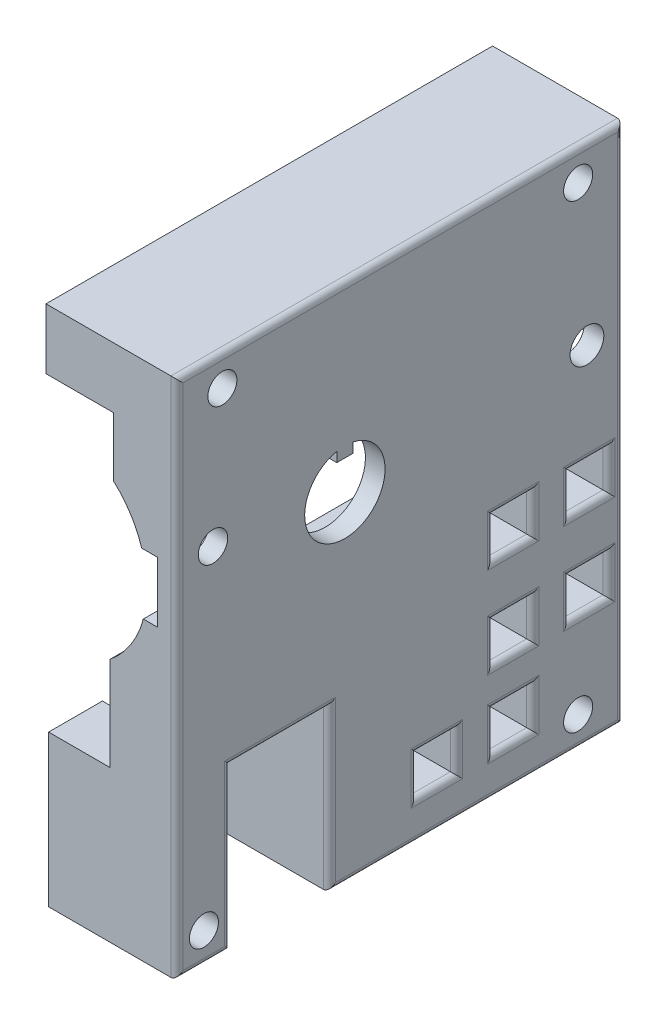
SolidWorks part; units mm, degrees
ref_plane "Front" through (0, 0, 0) normal (0, 0, 1) x (1, 0, 0)
ref_plane "Top" through (0, 0, 0) normal (0, 1, 0) x (1, 0, 0)
ref_plane "Right" through (0, 0, 0) normal (1, 0, 0) x (0, 0, -1)
sketch "Profile" plane through (0, 0, 0) normal (0, 0, 1) x (1, 0, 0)
  line L0 (-6.0107, -58.6279) -> (-6.0107, -33.6279)
  line L1 (-6.0107, -58.6279) -> (15.1893, -58.6279)
  line L2 (-6.4407, 17.4121) -> (-6.4407, 27.4121)
  line L3 (-6.4407, 27.4121) -> (15.1893, 27.4121)
  line L4 (15.1893, -58.6279) -> (15.1893, 27.4121)
  line L5 (-6.0107, -33.6279) -> (4.1393, -33.6279)
  line L6 (4.1393, -33.6279) -> (4.1393, -18.1379)
  line L7 (9.6313, -9.6379) -> (11.9493, -9.6379)
  line L8 (11.9493, -9.6379) -> (11.9493, 0.3621)
  line L9 (9.3593, 0.3621) -> (11.9493, 0.3621)
  line L10 (4.7093, 17.4121) -> (4.7093, 7.6371)
  line L11 (4.7093, 17.4121) -> (-6.4407, 17.4121)
  arc A0 (9.3593, 0.3621) -> (4.7093, 7.6371) centre (-6.1754, -4.4437) ccw
  arc A1 (4.1393, -18.1379) -> (9.6313, -9.6379) centre (-6.0948, -5.5013) ccw
  dimension "D14" = 16.261
  dimension "D17" = 16.261
  dimension "D2" = 10
  dimension "D3" = 2.59
  dimension "D4" = 2.318
  dimension "D5" = 9.775
  dimension "D6" = 11.15
  dimension "D7" = 15.49
  dimension "D8" = 10.15
  dimension "D9" = 25
  dimension "D10" = 21.2
  dimension "D11" = 86.04
  dimension "D12" = 21.63
  dimension "D13" = 10
  dimension "D15" = 23.99
  dimension "D16" = 5.492
extrude "ProfileExtrude" add sketch "Profile" along normal blind 73.76
sketch "HoseWindow" plane through (15.1893, 0, 0) normal (1, 0, 0) x (0, 0, -1)
  line L0 (-73.76, -58.6279) -> (0, -58.6279) construction
  line L1 (-64.87, -58.6279) -> (-48.58, -58.6279)
  line L2 (-64.87, -58.6279) -> (-64.87, -32.1279)
  line L3 (-64.87, -32.1279) -> (-48.58, -32.1279)
  line L4 (-48.58, -58.6279) -> (-48.58, -32.1279)
  line L5 (-73.76, -58.6279) -> (-73.76, 27.4121) construction
  dimension "D1" = 16.29
  dimension "D2" = 26.5
  dimension "D3" = 8.89
extrude "HoseWindowCut" cut sketch "HoseWindow" against normal through all
sketch "CageScrews" plane through (15.1893, 0, 0) normal (1, 0, 0) x (0, 0, -1)
  line L0 (-73.76, 27.4121) -> (0, 27.4121) construction
  line L1 (-73.76, -58.6279) -> (-73.76, 27.4121) construction
  line L2 (0, -58.6279) -> (0, 27.4121) construction
  line L3 (-48.58, -58.6279) -> (0, -58.6279) construction
  line L4 (-73.76, -58.6279) -> (-64.87, -58.6279) construction
  circle A0 centre (-66.26, 22.4121) radius 2.4
  circle A1 centre (-7.5, 22.4121) radius 2.4
  circle A2 centre (-7.5, -53.6279) radius 2.4
  circle A3 centre (-69.31, -53.6279) radius 2.4
  dimension "D1" = 4.8
  dimension "D2" = 4.8
  dimension "D3" = 4.8
  dimension "D4" = 4.8
  dimension "D5" = 5
  dimension "D6" = 7.5
  dimension "D7" = 7.5
  dimension "D8" = 5
  dimension "D9" = 5
  dimension "D10" = 7.5
  dimension "D11" = 5
  dimension "D12" = 4.45
extrude "CageScrewsCut" cut sketch "CageScrews" against normal through all
sketch "AxleHole" plane through (15.1893, 0, 0) normal (1, 0, 0) x (0, 0, -1)
  line L0 (-46.03, 2.3073) -> (-46.03, -9.2169) construction
  line L1 (-44.699, 2.3073) -> (-47.361, 2.3073)
  line L2 (-47.361, 2.3073) -> (-47.361, 3.9263)
  line L3 (-44.699, 2.3073) -> (-44.699, 3.9263)
  line L4 (-48.58, -58.6279) -> (0, -58.6279) construction
  line L5 (0, -58.6279) -> (0, 27.4121) construction
  arc A0 (-47.361, 3.9263) -> (-44.699, 3.9263) centre (-46.03, -2.5779) ccw
  dimension "D1" = 13.278
  dimension "D2" = 1.619
  dimension "D3" = 1.619
  dimension "D4" = 1.331
  dimension "D5" = 56.05
  dimension "D6" = 46.03
extrude "AxleHoleCut" cut sketch "AxleHole" against normal through all
sketch "SetScrews" plane through (15.1893, 0, 0) normal (1, 0, 0) x (0, 0, -1)
  line L0 (-46.03, -9.2169) -> (-46.03, -2.5779) construction
  circle A0 centre (-67.8072, 0.5449) radius 2.4263
  circle A1 centre (-6.043, -1.5582) radius 2.7888
  arc A3 (-47.361, 3.9263) -> (-44.699, 3.9263) centre (-46.03, -2.5779) ccw construction
  dimension "D1" = 22
  dimension "D2" = 40
extrude "SetScrewsCut" cut sketch "SetScrews" against normal through all
sketch "Sketch1" plane through (15.1893, 0, 0) normal (1, 0, 0) x (0, 0, -1)
  line L0 (-21.5, -45.7779) -> (-21.5, -52.2779)
  line L1 (-21.5, -45.7779) -> (-15, -45.7779)
  line L2 (-21.5, -52.2779) -> (-15, -52.2779)
  line L3 (-15, -45.7779) -> (-15, -52.2779)
  line L4 (0, -58.6279) -> (0, 27.4121) construction
  line L5 (-48.58, -58.6279) -> (0, -58.6279) construction
  line L6 (-34.1, -45.7779) -> (-27.6, -45.7779)
  line L7 (-34.1, -52.2779) -> (-27.6, -52.2779)
  line L8 (-34.1, -45.7779) -> (-34.1, -52.2779)
  line L9 (-27.6, -45.7779) -> (-27.6, -52.2779)
  line L10 (-8.9, -33.0779) -> (-2.4, -33.0779)
  line L11 (-8.9, -39.5779) -> (-2.4, -39.5779)
  line L12 (-8.9, -33.0779) -> (-8.9, -39.5779)
  line L13 (-2.4, -33.0779) -> (-2.4, -39.5779)
  line L14 (-21.5, -33.0779) -> (-15, -33.0779)
  line L15 (-21.5, -39.5779) -> (-15, -39.5779)
  line L16 (-21.5, -33.0779) -> (-21.5, -39.5779)
  line L17 (-15, -33.0779) -> (-15, -39.5779)
  line L18 (-21.5, -45.7779) -> (-34.1, -45.7779) construction
  line L19 (-8.9, -18.0779) -> (-2.4, -18.0779)
  line L20 (-8.9, -24.5779) -> (-2.4, -24.5779)
  line L21 (-8.9, -18.0779) -> (-8.9, -24.5779)
  line L22 (-2.4, -18.0779) -> (-2.4, -24.5779)
  line L23 (-21.5, -18.0779) -> (-15, -18.0779)
  line L24 (-21.5, -24.5779) -> (-15, -24.5779)
  line L25 (-21.5, -18.0779) -> (-21.5, -24.5779)
  line L26 (-15, -18.0779) -> (-15, -24.5779)
  line L27 (-21.5, -33.0779) -> (-8.9, -33.0779) construction
  line L42 (-34.1, -33.0779) -> (-27.6, -33.0779) [skipped]
  line L43 (-34.1, -39.5779) -> (-27.6, -39.5779) [skipped]
  line L44 (-34.1, -33.0779) -> (-34.1, -39.5779) [skipped]
  line L45 (-27.6, -33.0779) -> (-27.6, -39.5779) [skipped]
  dimension "D1" = 15
  dimension "D2" = 6.5
  dimension "D3" = 6.5
  dimension "D4" = 6.35
  dimension "D5" = 12.6
  dimension "D6" = 12.6
extrude "Cut-Extrude1" cut sketch "Sketch1" against normal through all
fillet "Fillet1" radius 1 32 edges at (15.1893, -49.0279, 21.5) (15.1893, -52.2779, 18.25) (15.1893, -49.0279, 15) (15.1893, -45.7779, 18.25) (15.1893, -58.6279, 69.315) (15.1893, -45.3779, 64.87) (15.1893, -32.1279, 56.725) (15.1893, -45.3779, 48.58) (15.1893, -58.6279, 24.29) (15.1893, -15.6079, 0) (15.1893, 27.4121, 36.88) (15.1893, -15.6079, 73.76) (15.1893, -24.5779, 5.65) (15.1893, -21.3279, 2.4) (15.1893, -18.0779, 5.65) (15.1893, -21.3279, 8.9) (15.1893, -21.3279, 15) (15.1893, -18.0779, 18.25) (15.1893, -21.3279, 21.5) (15.1893, -24.5779, 18.25) (15.1893, -39.5779, 5.65) (15.1893, -36.3279, 2.4) (15.1893, -33.0779, 5.65) (15.1893, -36.3279, 8.9) (15.1893, -36.3279, 15) (15.1893, -33.0779, 18.25) (15.1893, -36.3279, 21.5) (15.1893, -39.5779, 18.25) (15.1893, -52.2779, 30.85) (15.1893, -49.0279, 27.6) (15.1893, -45.7779, 30.85) (15.1893, -49.0279, 34.1)
equation "\"BottomEdge\"=21.20mm"
equation "\"TopEdge\"=21.63mm"
equation "\"TotalHeight\"=86.04mm"
equation "\"TotalLength\"=73.76mm"
equation "\"Screw Clearance\" = 10mm"
equation "\"TopDepth\"= 11.15mm"
equation "\"BottomDepth\"=10.15mm"
equation "\"TopHeight\"=9.775mm"
equation "\"BottomHeight\"=15.49mm"
equation "\"TopChannelDepth\"=2.59mm"
equation "\"BottomChannelDepth\"=2.318mm"
equation "\"ChannelHeight\"=10mm"
equation "\"ChamberRadius\"=16.261mm"
equation "\"ChanRelHeight\"=23.99mm"
equation "\"ChanRelDepth\"=5.492mm"
equation "\"D2@Profile\"= \"ChannelHeight\""
equation "\"D4@Profile\"= \"BottomChannelDepth\""
equation "\"D3@Profile\"= \"TopChannelDepth\""
equation "\"D5@Profile\"= \"TopHeight\""
equation "\"D7@Profile\"= \"BottomHeight\""
equation "\"ScrewClearanceBottom\" = 25mm"
equation "\"D9@Profile\"=\"ScrewClearanceBottom\""
equation "\"D13@Profile\"= \"Screw Clearance\""
equation "\"D8@Profile\"= \"BottomDepth\""
equation "\"D6@Profile\"= \"TopDepth\""
equation "\"D10@Profile\"=\"BottomEdge\""
equation "\"D12@Profile\"= \"TopEdge\""
equation "\"D11@Profile\"= \"TotalHeight\""
equation "\"D15@Profile\"= \"ChanRelHeight\""
equation "\"D16@Profile\"= \"ChanRelDepth\""
equation "\"D17@Profile\"= \"ChamberRadius\""
equation "\"D14@Profile\"= \"ChamberRadius\""
equation "\"D1@ProfileExtrude\"= \"TotalLength\""
equation "\"CageScrewDiameter\"=4.8mm"
equation "\"SetScrewDiameter\"=3.5mm"
equation "\"AxleRadius\"=6.639mm"
equation "\"KeyHeight\"=1.619mm"
equation "\"KeyWidth\"=2.662mm"
equation "\"HoseWindowWidth\"=16.29mm"
equation "\"HoseWindowHeight\"=26.5mm"
equation "\"HoseWindow-Edge\"=8.89mm"
equation "\"CageScrew-VerticalEdge\"=5.0mm"
equation "\"CageScrew-HorizontalEdge\"=7.5mm"
equation "\"CageScrew-HoseCornerScrewEdge\"=4.45mm"
equation "\"Axle-BottomEdge\"=56.05mm"
equation "\"Axle-FrontEdge\"=46.03mm"
equation "\"FrontSetScrew-Axel\"=40mm"
equation "\"D1@HoseWindow\"= \"HoseWindowWidth\""
equation "\"D2@HoseWindow\"= \"HoseWindowHeight\""
equation "\"D3@HoseWindow\"= \"HoseWindow-Edge\""
equation "\"D6@CageScrews\"= \"CageScrew-HorizontalEdge\""
equation "\"D7@CageScrews\"= \"CageScrew-HorizontalEdge\""
equation "\"D10@CageScrews\"= \"CageScrew-HorizontalEdge\""
equation "\"D12@CageScrews\"= \"CageScrew-HoseCornerScrewEdge\""
equation "\"D5@CageScrews\"= \"CageScrew-VerticalEdge\""
equation "\"D8@CageScrews\"= \"CageScrew-VerticalEdge\""
equation "\"D11@CageScrews\"= \"CageScrew-VerticalEdge\""
equation "\"D9@CageScrews\"= \"CageScrew-VerticalEdge\""
equation "\"D1@CageScrews\"= \"CageScrewDiameter\""
equation "\"D2@CageScrews\"= \"CageScrewDiameter\""
equation "\"D4@CageScrews\"= \"CageScrewDiameter\""
equation "\"D3@CageScrews\"= \"CageScrewDiameter\""
equation "\"D1@AxleHole\"= \"AxleRadius\" * 2"
equation "\"D3@AxleHole\"= \"KeyHeight\""
equation "\"D2@AxleHole\"= \"KeyHeight\""
equation "\"D4@AxleHole\"= \"KeyWidth\" / 2"
equation "\"D6@AxleHole\"= \"Axle-FrontEdge\""
equation "\"D5@AxleHole\"= \"Axle-BottomEdge\""
equation "\"D2@SetScrews\"= \"FrontSetScrew-Axel\""
equation "\"BackSetScrew-Axel\"=22mm"
equation "\"D1@SetScrews\"= \"BackSetScrew-Axel\""
equation "\"SlotFront\"=15mm"
equation "\"D1@Sketch1\"=\"SlotFront\""
equation "\"Slot\"=6.5mm"
equation "\"D2@Sketch1\"=\"Slot\""
equation "\"D3@Sketch1\"=\"Slot\""
equation "\"SlotBottom\"=6.35mm"
equation "\"D4@Sketch1\"=\"SlotBottom\""
